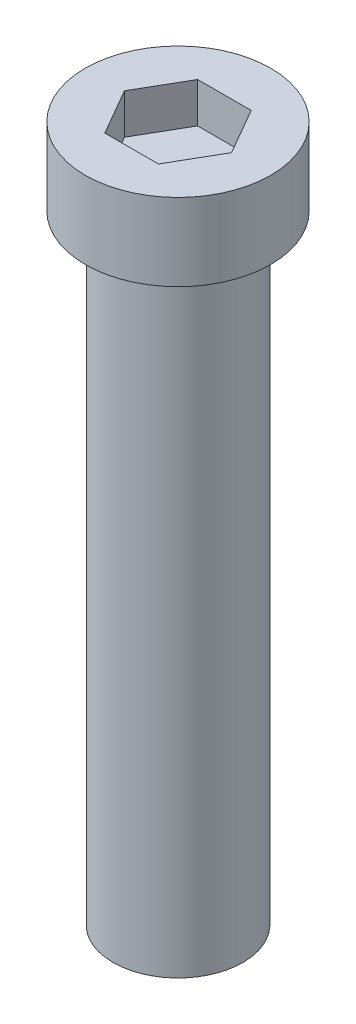
SolidWorks part; units mm, degrees
material "201 Acero inoxidable recocido (SS)"
ref_plane "Alzado" through (0, 0, 0) normal (0, 0, 1) x (1, 0, 0)
ref_plane "Planta" through (0, 0, 0) normal (0, 1, 0) x (1, 0, 0)
ref_plane "Vista lateral" through (0, 0, 0) normal (1, 0, 0) x (0, 0, -1)
sketch "Croquis1" plane through (0, 0, 0) normal (0, 1, 0) x (1, 0, 0)
  circle A0 centre (0, 0) radius 3
  dimension "D1" = 6
extrude "Saliente-Extruir1" add sketch "Croquis1" along normal blind 2.5
sketch "Croquis2" plane through (0, 0, 0) normal (0, 1, 0) x (1, 0, 0)
  circle A0 centre (0, 0) radius 2.1
  dimension "D1" = 4.2
extrude "Saliente-Extruir2" add sketch "Croquis2" against normal blind 20
ref_plane "Plano1" through (0, 3.7, 0) normal (0, 1, 0) x (1, 0, 0)
sketch "Croquis4" plane through (0, 3.7, 0) normal (0, 1, 0) x (1, 0, 0)
  line L1 (1.7321, 0) -> (0.866, 1.5)
  line L2 (0.866, 1.5) -> (-0.866, 1.5)
  line L3 (-0.866, 1.5) -> (-1.7321, 0)
  line L4 (-1.7321, 0) -> (-0.866, -1.5)
  line L5 (-0.866, -1.5) -> (0.866, -1.5)
  line L6 (0.866, -1.5) -> (1.7321, 0)
  circle A0 centre (0, 0) radius 1.5 construction
  dimension "D1" = 3
extrude "Cortar-Extruir1" cut sketch "Croquis4" against normal blind 2.5
